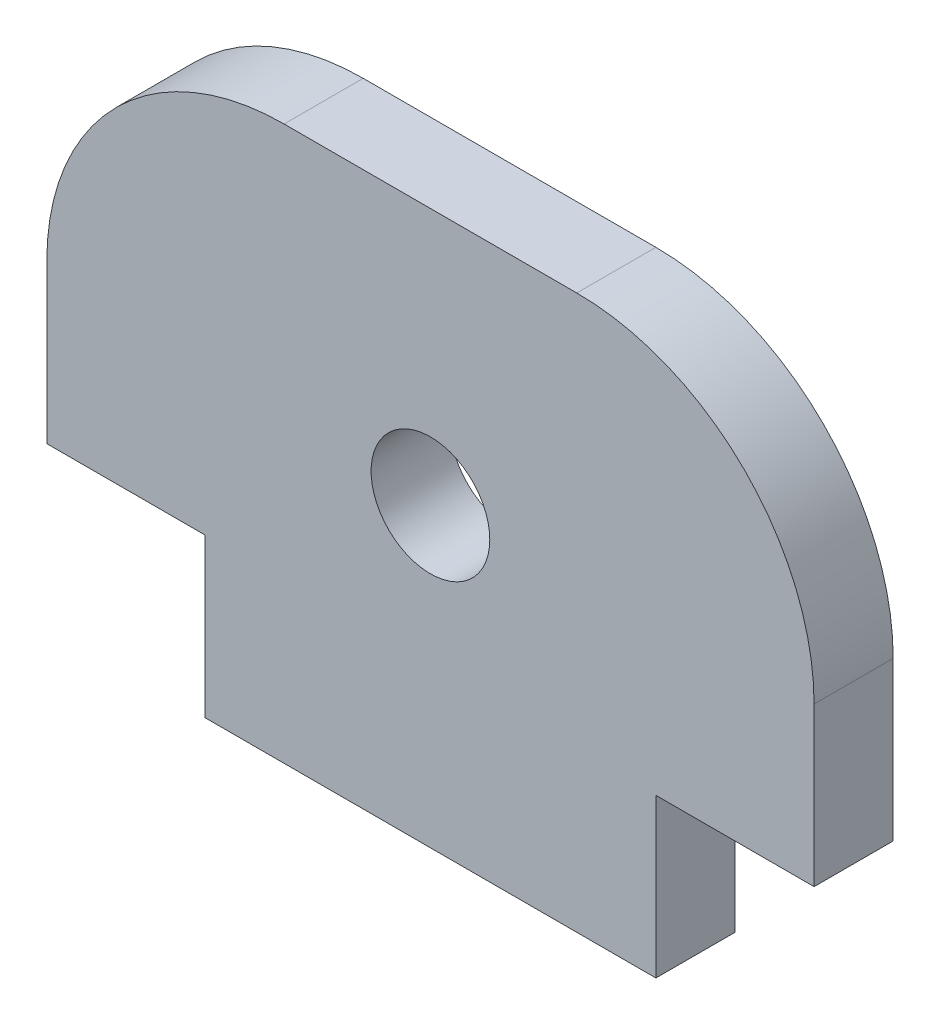
SolidWorks part; units mm, degrees
material "Acrylic (Medium-high impact)"
ref_plane "Front Plane" through (0, 0, 0) normal (0, 0, 1) x (1, 0, 0)
ref_plane "Top Plane" through (0, 0, 0) normal (0, 1, 0) x (1, 0, 0)
ref_plane "Right Plane" through (0, 0, 0) normal (1, 0, 0) x (0, 0, -1)
sketch "Model" plane through (0, 0, 0) normal (0, 0, 1) x (1, 0, 0)
  line L100 (9.7, -3.5) -> (9.7, 0.5)
  line L101 (-9.7, -3.5) -> (-9.7, 0.5)
  line L102 (-9.7, -3.5) -> (-5.7, -3.5)
  line L103 (9.7, -3.5) -> (5.7, -3.5)
  line L104 (-3.7, 6.5) -> (3.7, 6.5)
  line L582 (5.7, -3.5) -> (5.7, -7.5)
  line L583 (5.7, -7.5) -> (-5.7, -7.5)
  line L584 (-5.7, -7.5) -> (-5.7, -3.5)
  arc A49 (9.7, 0.5) -> (3.7, 6.5) centre (3.7, 0.5) ccw
  arc A50 (-3.7, 6.5) -> (-9.7, 0.5) centre (-3.7, 0.5) ccw
  circle A53 centre (0, 0) radius 1.5
  dimension "D1" = 3
  dimension "D2" = 6
  dimension "D3" = 5.7
  dimension "D4" = 9.7
  dimension "D5" = 5.7
  dimension "D6" = 6.5
extrude "Boss-Extrude1" add sketch "Model" along normal blind 2
